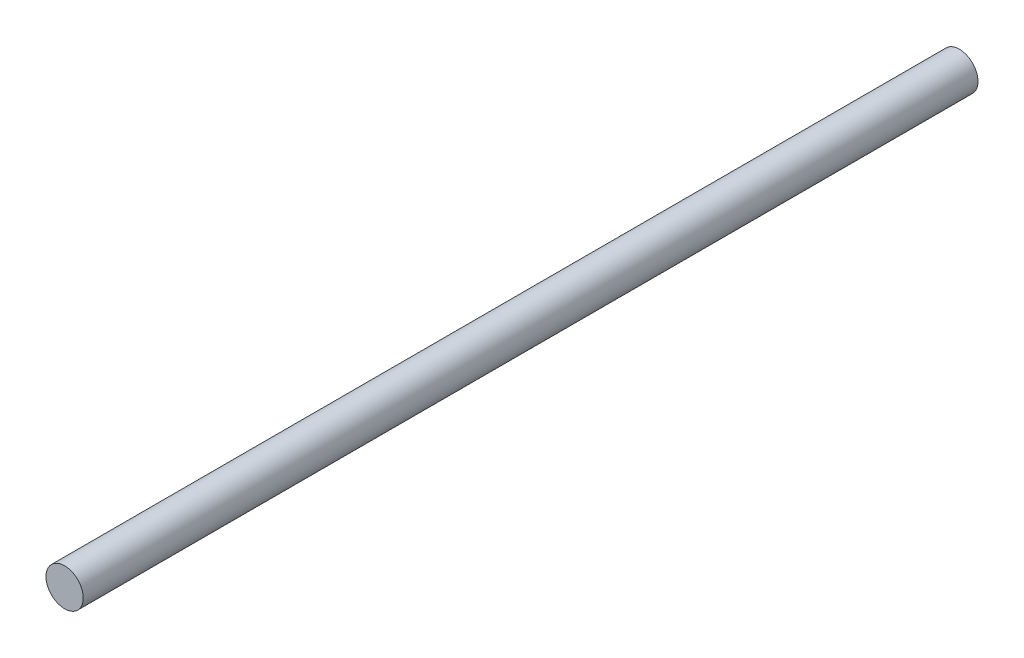
SolidWorks part; units mm, degrees
ref_plane "Front Plane" through (0, 0, 0) normal (0, 0, 1) x (1, 0, 0)
ref_plane "Top Plane" through (0, 0, 0) normal (0, 1, 0) x (1, 0, 0)
ref_plane "Right Plane" through (0, 0, 0) normal (1, 0, 0) x (0, 0, -1)
sketch "Sketch1" plane through (0, 0, 0) normal (0, 0, 1) x (1, 0, 0)
  circle A0 centre (0, 0) radius 6.35
  dimension "D1" = 12.7
extrude "Boss-Extrude1" add sketch "Sketch1" along normal mid plane 304.8
